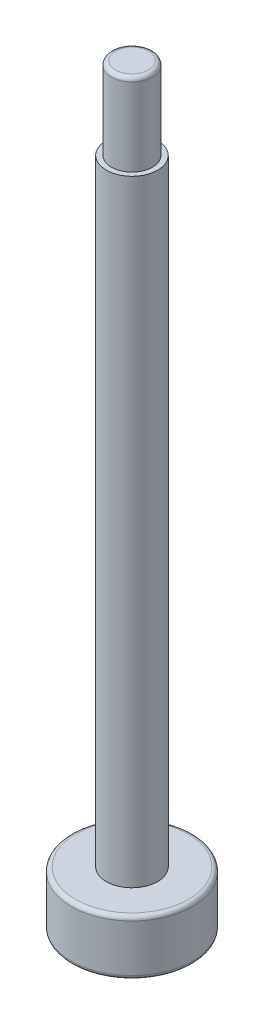
SolidWorks part; units mm, degrees
ref_plane "前视基准面" through (0, 0, 0) normal (0, 0, 1) x (1, 0, 0)
ref_plane "上视基准面" through (0, 0, 0) normal (0, 1, 0) x (1, 0, 0)
ref_plane "右视基准面" through (0, 0, 0) normal (1, 0, 0) x (0, 0, -1)
sketch "草图1" plane through (0, 0, 0) normal (0, 1, 0) x (1, 0, 0)
  circle A0 centre (0, 0) radius 2.95
  dimension "D1" = 5.9
extrude "凸台-拉伸1" add sketch "草图1" along normal blind 2.7
sketch "草图2" plane through (0, 2.7, 0) normal (0, 1, 0) x (1, 0, 0)
  circle A0 centre (0, 0) radius 1.25
  dimension "D1" = 2.5
extrude "凸台-拉伸2" add sketch "草图2" along normal blind 30
sketch "草图3" plane through (0, 32.7, 0) normal (0, 1, 0) x (1, 0, 0)
  circle A0 centre (0, 0) radius 1
  dimension "D1" = 2
extrude "凸台-拉伸3" add sketch "草图3" along normal blind 4
sketch "草图4" plane through (0, 0, 0) normal (0, -1, 0) x (1, 0, 0)
  line L1 (2.2473, -0.532) -> (1.5844, 1.6802)
  line L2 (1.5844, 1.6802) -> (-0.6629, 2.2122)
  line L3 (-0.6629, 2.2122) -> (-2.2473, 0.532)
  line L4 (-2.2473, 0.532) -> (-1.5844, -1.6802)
  line L5 (-1.5844, -1.6802) -> (0.6629, -2.2122)
  line L6 (0.6629, -2.2122) -> (2.2473, -0.532)
  circle A0 centre (0, 0) radius 2 construction
  dimension "D1" = 4
extrude "切除-拉伸1" cut sketch "草图4" against normal blind 2
fillet "圆角1" radius 0.2 3 edges at (0, 0, 2.95) (0, 2.7, 2.95) (0, 36.7, 1)
